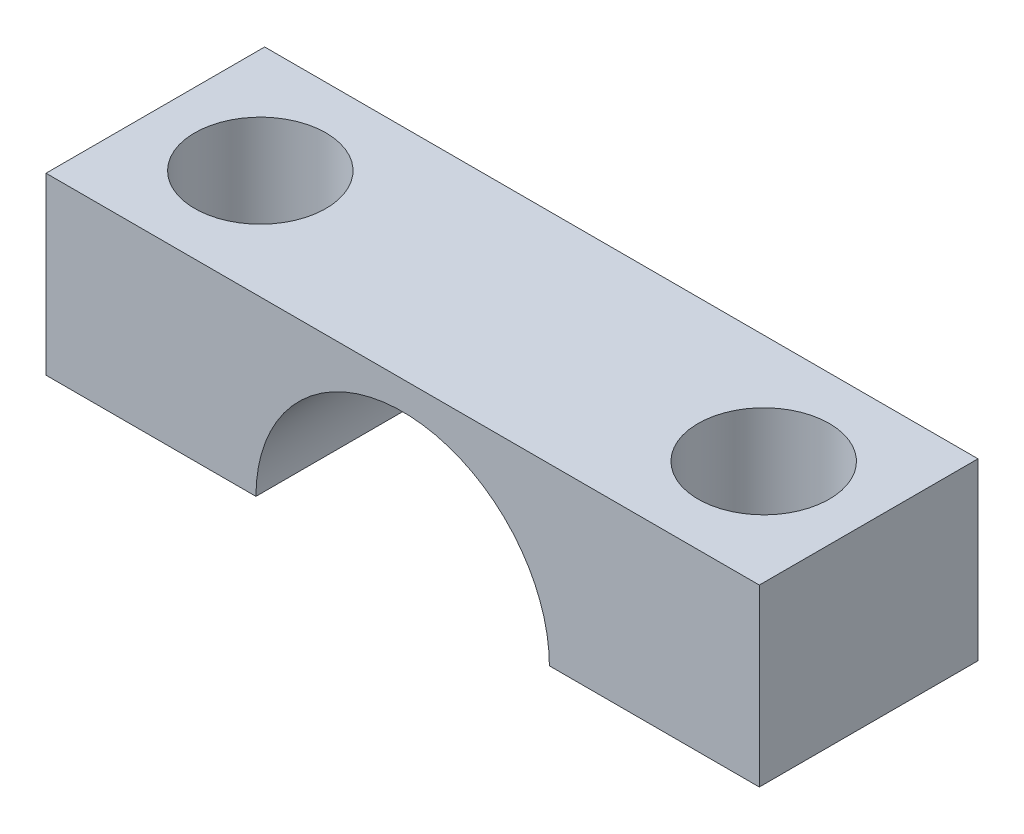
SolidWorks part; units mm, degrees
material "6061-T6 (SS)"
ref_plane "Front Plane" through (0, 0, 0) normal (0, 0, 1) x (1, 0, 0)
ref_plane "Top Plane" through (0, 0, 0) normal (0, 1, 0) x (1, 0, 0)
ref_plane "Right Plane" through (0, 0, 0) normal (1, 0, 0) x (0, 0, -1)
sketch "Sketch1" plane through (0, 0, 0) normal (0, 0, 1) x (1, 0, 0)
  line L1 (-8.155, -2) -> (8.155, -2)
  line L2 (-8.155, -2) -> (-8.155, 2)
  line L3 (-8.155, 2) -> (8.155, 2)
  line L4 (8.155, -2) -> (8.155, 2)
  line L5 (-8.155, -2) -> (8.155, 2) construction
  line L6 (-8.155, 2) -> (8.155, -2) construction
  point P0 (0, 0)
  dimension "D1" = 4
  dimension "D2" = 16.31
sketch "Sketch3" plane through (0, 0, 0) normal (0, 0, 1) x (1, 0, 0)
  line L0 (0, 0) -> (0, -2) construction
  line L1 (-8.155, -2) -> (8.155, -2) construction
  line L2 (-3.355, -2) -> (3.355, -2)
  line L3 (0, 1.355) -> (0, 2) construction
  line L4 (-8.155, 2) -> (8.155, 2) construction
  arc A0 (3.355, -2) -> (-3.355, -2) centre (0, -2) ccw
  point P8 (0, -2)
extrude "Boss-Extrude3" add sketch "Sketch1" against normal blind 5 contours L2 L3 L4 L1
extrude "Cut-Extrude9" cut sketch "Sketch3" against normal blind 5
sketch "Sketch4" plane through (0, 0, 0) normal (0, 1, 0) x (1, 0, 0)
  line L0 (0, 0) -> (0, 5) construction
  line L1 (-8.155, 0) -> (8.155, 0) construction
  line L2 (-8.155, 5) -> (8.155, 5) construction
  line L3 (0, 2.5) -> (5.755, 2.5) construction
  line L5 (0, 2.5) -> (-5.755, 2.5) construction
  circle A0 centre (-5.755, 2.5) radius 1.5
  circle A1 centre (5.755, 2.5) radius 1.5
extrude "Cut-Extrude10" cut sketch "Sketch4" against normal blind 2.5 and the other way blind 2.5 from offset 0
